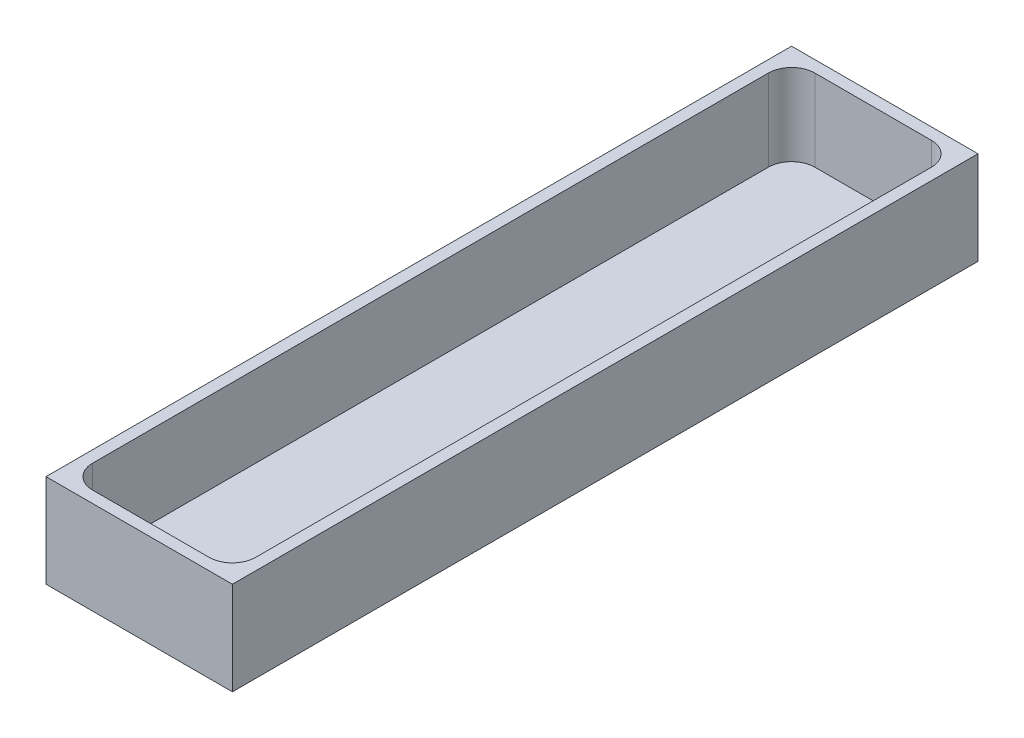
SolidWorks part; units mm, degrees
material "6061-T6 (SS)"
ref_plane "Front Plane" through (0, 0, 0) normal (0, 0, 1) x (1, 0, 0)
ref_plane "Top Plane" through (0, 0, 0) normal (0, 1, 0) x (1, 0, 0)
ref_plane "Right Plane" through (0, 0, 0) normal (1, 0, 0) x (0, 0, -1)
sketch "Sketch1" plane through (0, 0, 0) normal (0, 1, 0) x (1, 0, 0)
  line L1 (0, 0) -> (50.8, 0)
  line L2 (0, 0) -> (0, 203.2)
  line L3 (0, 203.2) -> (50.8, 203.2)
  line L4 (50.8, 0) -> (50.8, 203.2)
  dimension "D1" = 203.2
  dimension "D2" = 50.8
extrude "Boss-Extrude1" add sketch "Sketch1" along normal blind 25.4
shell "Shell1" thickness 3.175
fillet "Fillet1" radius 6.35 4 edges at (3.175, 14.2875, -3.175) (47.625, 14.2875, -3.175) (47.625, 14.2875, -200.025) (3.175, 14.2875, -200.025)
